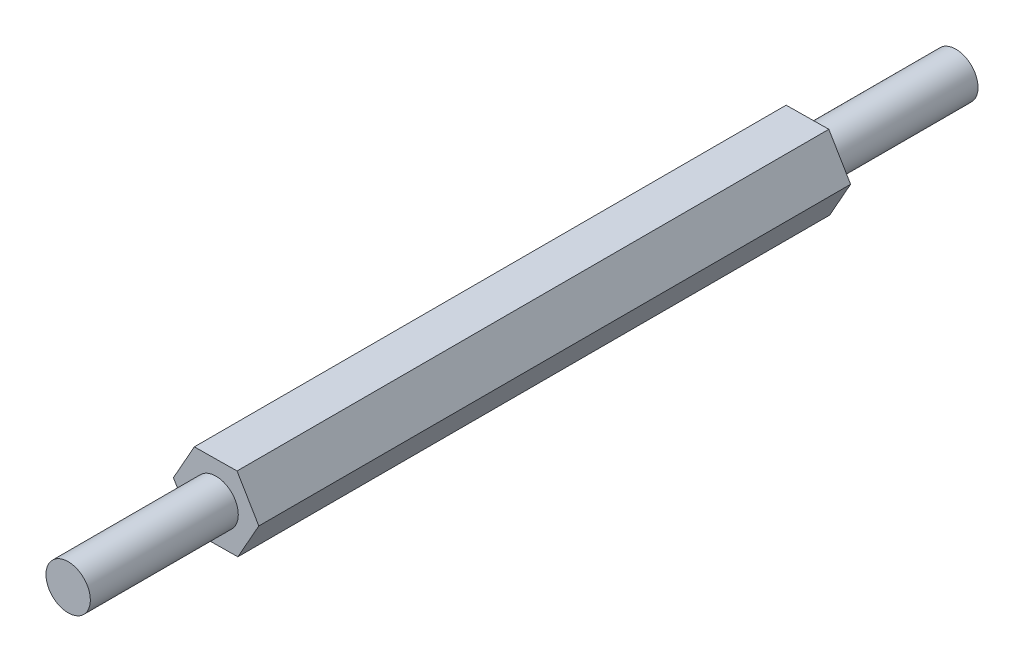
SolidWorks part; units mm, degrees
ref_plane "Plan de face" through (0, 0, 0) normal (0, 0, 1) x (1, 0, 0)
ref_plane "Plan de dessus" through (0, 0, 0) normal (0, 1, 0) x (1, 0, 0)
ref_plane "Plan de droite" through (0, 0, 0) normal (1, 0, 0) x (0, 0, -1)
sketch "Esquisse1" plane through (0, 0, 0) normal (0, 0, 1) x (1, 0, 0)
  line L1 (1.4705, -2.4842) -> (2.8866, 0.0314)
  line L2 (2.8866, 0.0314) -> (1.4161, 2.5155)
  line L3 (1.4161, 2.5155) -> (-1.4705, 2.4842)
  line L4 (-1.4705, 2.4842) -> (-2.8866, -0.0314)
  line L5 (-2.8866, -0.0314) -> (-1.4161, -2.5155)
  line L6 (-1.4161, -2.5155) -> (1.4705, -2.4842)
  circle A0 centre (0, 0) radius 2.5 construction
  dimension "D1" = 5
extrude "Boss.-Extru.1" add sketch "Esquisse1" along normal blind 40
sketch "Esquisse2" plane through (0, 0, 40) normal (0, 0, 1) x (1, 0, 0)
  circle A0 centre (0, 0) radius 1.5
  dimension "D1" = 3
extrude "Boss.-Extru.2" add sketch "Esquisse2" along normal blind 10
sketch "Esquisse3" plane through (0, 0, 0) normal (0, 0, -1) x (-1, 0, 0)
  circle A0 centre (0, 0) radius 1.5
  dimension "D1" = 3
extrude "Boss.-Extru.3" add sketch "Esquisse3" along normal blind 10
